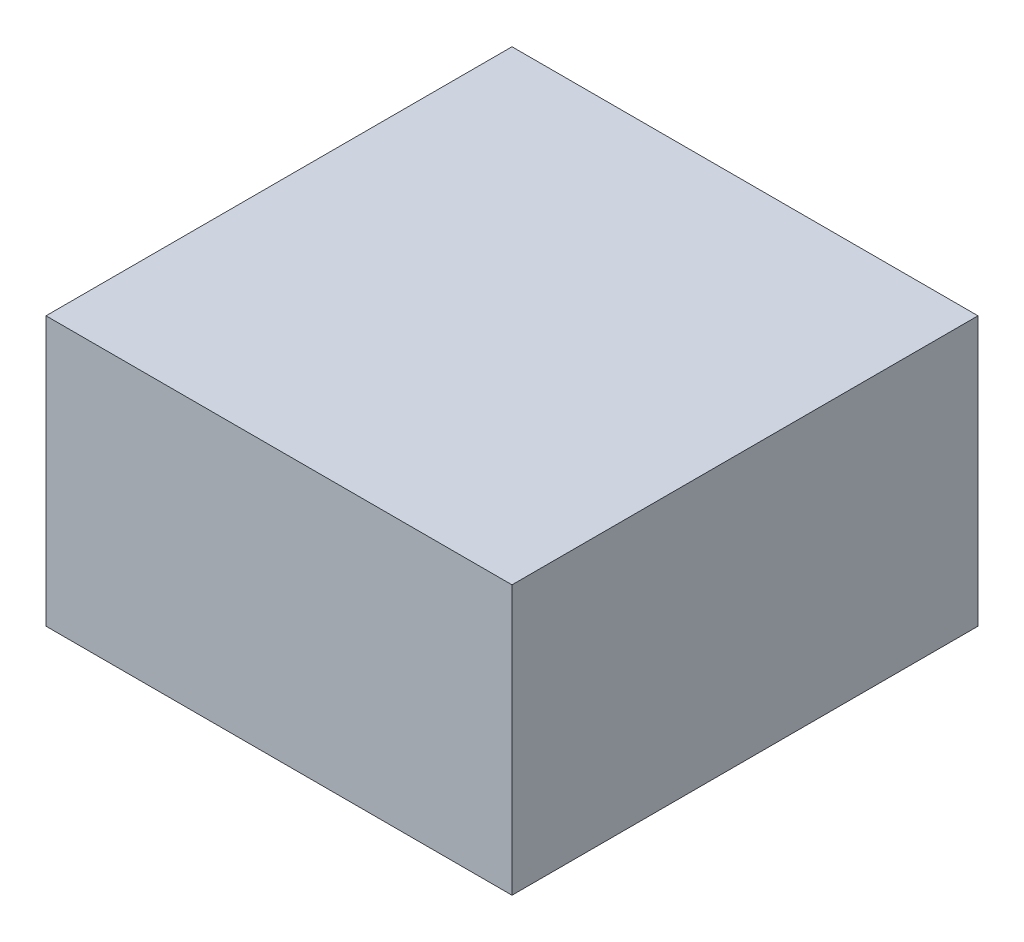
SolidWorks part; units mm, degrees
material "1060 Alloy"
ref_plane "Front Plane" through (0, 0, 0) normal (0, 0, 1) x (1, 0, 0)
ref_plane "Top Plane" through (0, 0, 0) normal (0, 1, 0) x (1, 0, 0)
ref_plane "Right Plane" through (0, 0, 0) normal (1, 0, 0) x (0, 0, -1)
sketch "Sketch1" plane through (0, 0, 0) normal (0, 1, 0) x (1, 0, 0)
  line L1 (0, 0) -> (99.06, 0)
  line L2 (0, 0) -> (0, 99.06)
  line L3 (0, 99.06) -> (99.06, 99.06)
  line L4 (99.06, 0) -> (99.06, 99.06)
  dimension "D1" = 99.06
  dimension "D2" = 99.06
extrude "Boss-Extrude1" add sketch "Sketch1" along normal blind 57.15
